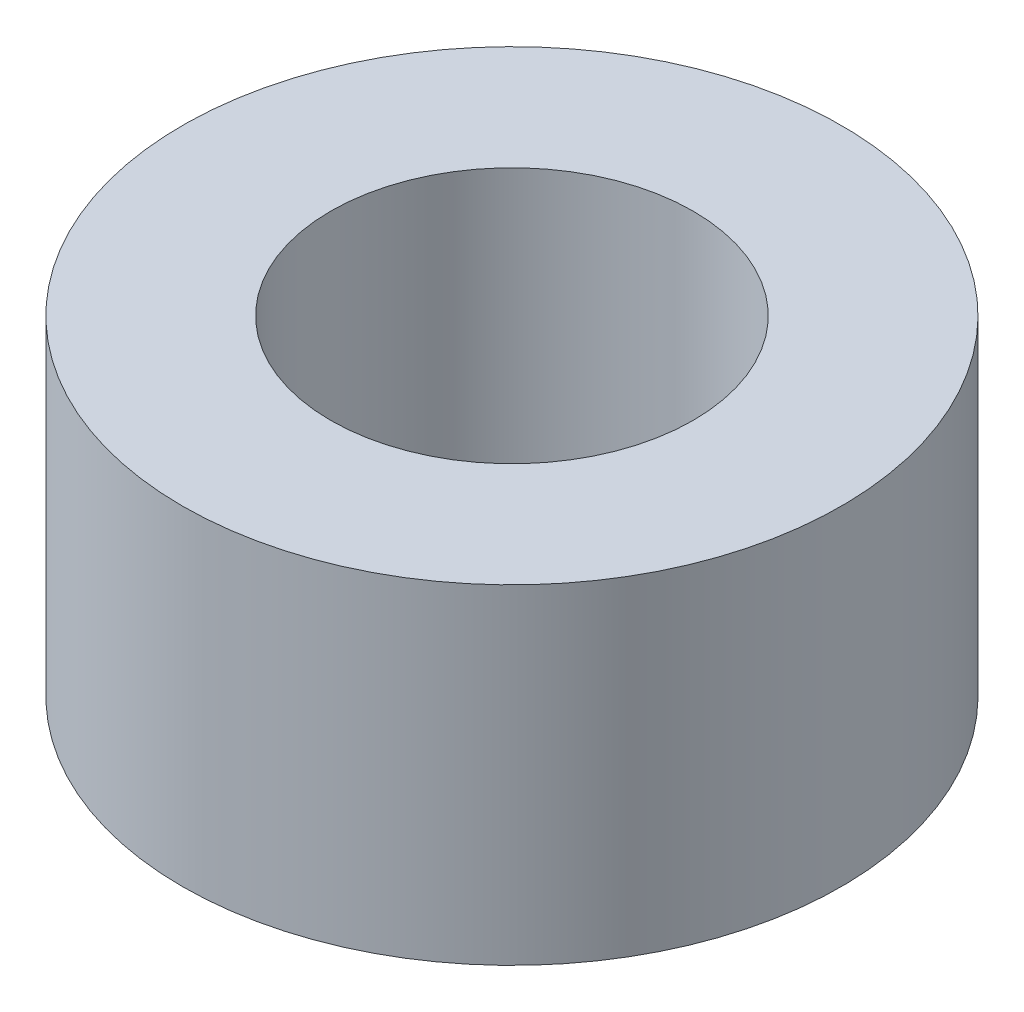
SolidWorks part; units mm, degrees
material "尼龙(白)"
ref_plane "前视基准面" through (0, 0, 0) normal (0, 0, 1) x (1, 0, 0)
ref_plane "上视基准面" through (0, 0, 0) normal (0, 1, 0) x (1, 0, 0)
ref_plane "右视基准面" through (0, 0, 0) normal (1, 0, 0) x (0, 0, -1)
sketch "草图2" plane through (0, 0, 0) normal (0, 1, 0) x (1, 0, 0)
  circle A0 centre (0, 0) radius 15
  dimension "D1" = 30
extrude "凸台-拉伸1" add sketch "草图2" along normal blind 15
hole_wizard "M18x1.0 螺纹孔1" positions "草图4" profile "草图3" tap size "M18x1.0" standard "GB" end condition through all
sketch "草图4" plane through (0, 15, 0) normal (0, 1, 0) x (1, 0, 0)
  point P0 (0, 0)
sketch "草图3" plane through (0, 15, 0) normal (1, 0, 0) x (0, 0, 1)
  line L0 (0, 0) -> (0, 15)
  line L1 (0, 15) -> (8.25, 15)
  line L2 (8.25, 15) -> (8.25, 0)
  line L5 (8.25, 0) -> (0, 0)
  line L11 (0, -6.35) -> (0, 107.95) construction
  dimension "通孔螺纹孔钻头直径" = 16.5
  dimension "通孔螺纹孔钻头深度" = 15
cosmetic thread "孔螺蚊线1"
